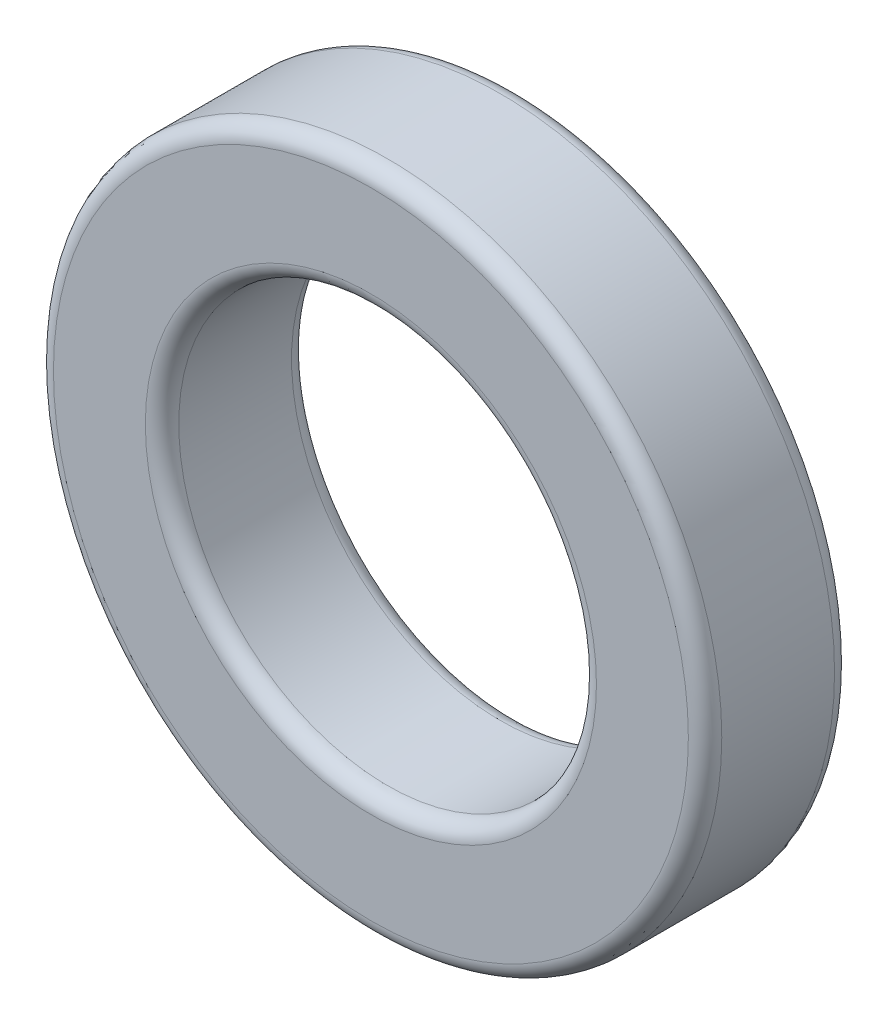
SolidWorks part; units mm, degrees
ref_plane "Front Plane" through (0, 0, 0) normal (0, 0, 1) x (1, 0, 0)
ref_plane "Top Plane" through (0, 0, 0) normal (0, 1, 0) x (1, 0, 0)
ref_plane "Right Plane" through (0, 0, 0) normal (1, 0, 0) x (0, 0, -1)
sketch "Sketch1" plane through (0, 0, 0) normal (0, 0, 1) x (1, 0, 0)
  circle A0 centre (0, 0) radius 10
  circle A1 centre (0, 0) radius 16
  dimension "D1" = 20
  dimension "D2" = 32
extrude "Boss-Extrude1" add sketch "Sketch1" along normal blind 7
fillet "Fillet1" radius 0.8 4 edges at (10, 0, 7) (10, 0, 0) (16, 0, 7) (16, 0, 0)
